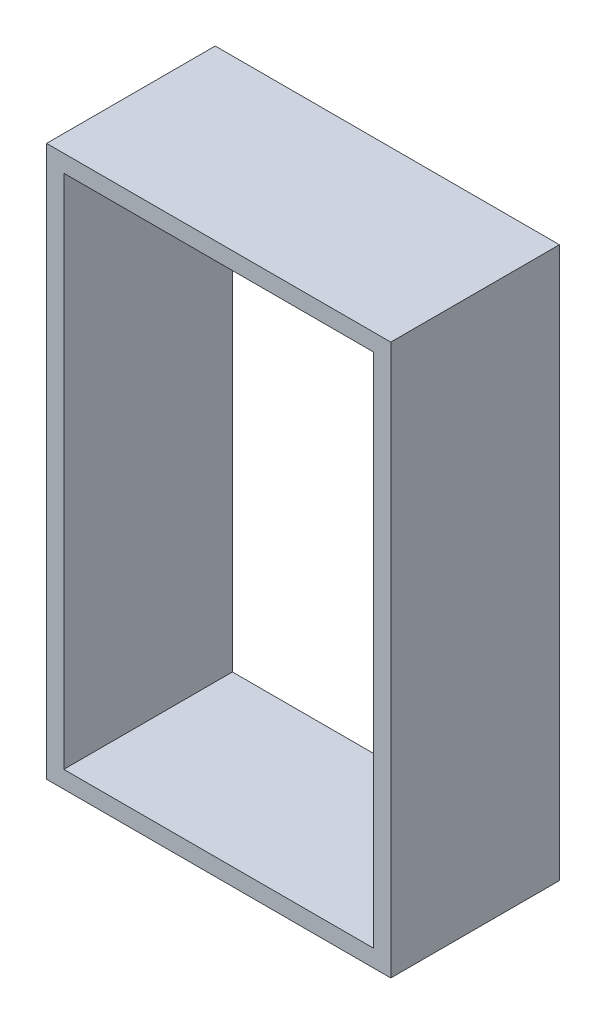
SolidWorks part; units mm, degrees
ref_plane "Front Plane" through (0, 0, 0) normal (0, 0, 1) x (1, 0, 0)
ref_plane "Top Plane" through (0, 0, 0) normal (0, 1, 0) x (1, 0, 0)
ref_plane "Right Plane" through (0, 0, 0) normal (1, 0, 0) x (0, 0, -1)
sketch "Sketch1" plane through (0, 0, 0) normal (0, 0, 1) x (1, 0, 0)
  line L0 (6.35, 196.85) -> (120.65, 196.85)
  line L1 (0, 0) -> (127, 0)
  line L2 (0, 0) -> (0, 203.2)
  line L3 (0, 203.2) -> (127, 203.2)
  line L4 (127, 0) -> (127, 203.2)
  line L5 (120.65, 6.35) -> (120.65, 196.85)
  line L6 (6.35, 6.35) -> (120.65, 6.35)
  line L7 (6.35, 6.35) -> (6.35, 196.85)
  dimension "D1" = 203.2
  dimension "D2" = 127
  dimension "D3" = 6.35
extrude "Boss-Extrude1" add sketch "Sketch1" along normal blind 62.23
